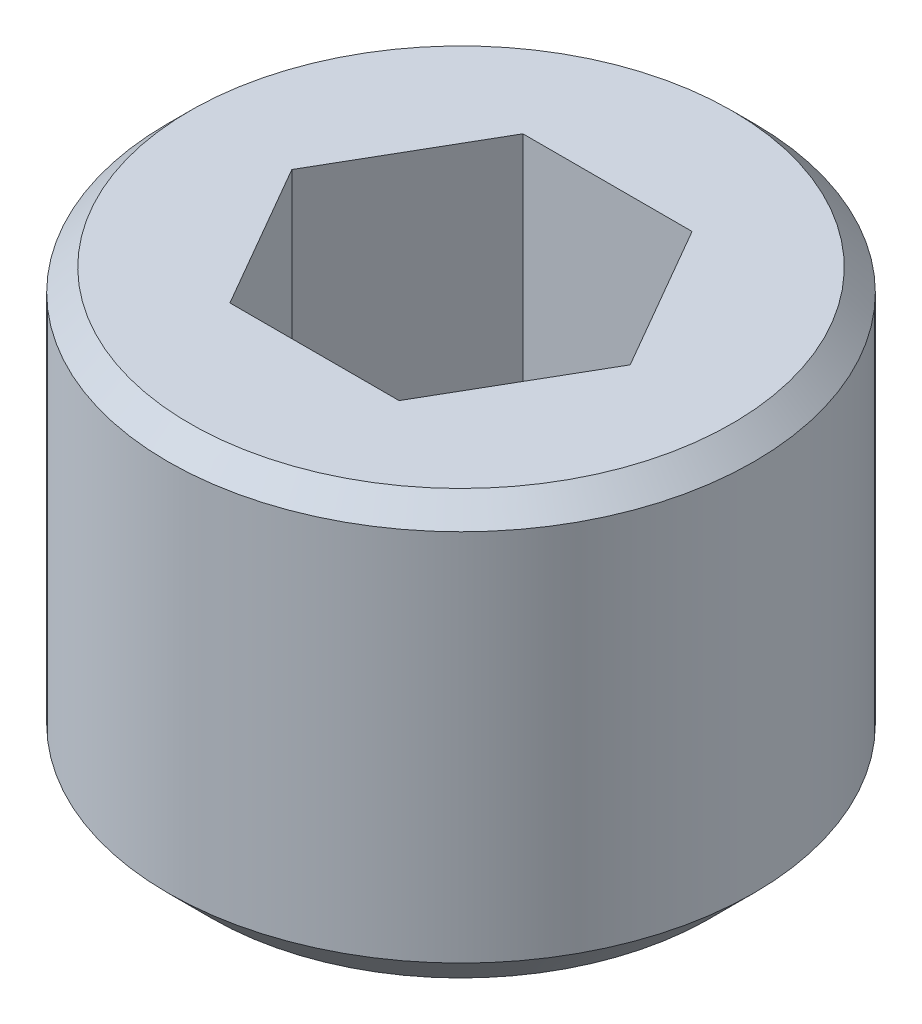
SolidWorks part; units mm, degrees
material "acero"
ref_plane "Alzado" through (0, 0, 0) normal (0, 0, 1) x (1, 0, 0)
ref_plane "Planta" through (0, 0, 0) normal (0, 1, 0) x (1, 0, 0)
ref_plane "Vista lateral" through (0, 0, 0) normal (1, 0, 0) x (0, 0, -1)
sketch "Croquis1" plane through (0, 0, 0) normal (0, 0, 1) x (1, 0, 0)
  line L0 (0, 0) -> (0, -60.9498) construction
  line L1 (0, 0) -> (2, 0)
  line L4 (2, 0) -> (2, -3)
  line L5 (2, -3) -> (0, -3)
  line L6 (0, -3) -> (0, 0)
  dimension "D1" = 3
  dimension "D4" = 4
revolve "Revolución1" add sketch "Croquis1" angle 360 about L0
cosmetic thread "Rosca cosmética1" parameters "D2"=3.22
sketch "Croquis3" plane through (0, 0, 0) normal (0, 1, 0) x (1, 0, 0)
  line L1 (-0.5774, 1) -> (-1.1547, 0)
  line L2 (-1.1547, 0) -> (-0.5774, -1)
  line L3 (-0.5774, -1) -> (0.5774, -1)
  line L4 (0.5774, -1) -> (1.1547, 0)
  line L5 (1.1547, 0) -> (0.5774, 1)
  line L6 (0.5774, 1) -> (-0.5774, 1)
  circle A0 centre (0, 0) radius 1 construction
  dimension "D1" = 2
extrude "Cortar-Extruir2" cut sketch "Croquis3" against normal blind 2
chamfer "Chaflán3" distance 0.3 angle 45 1 edges at (0, -3, 2)
chamfer "Chaflán4" distance 0.15 angle 45 1 edges at (0, 0, 2)
